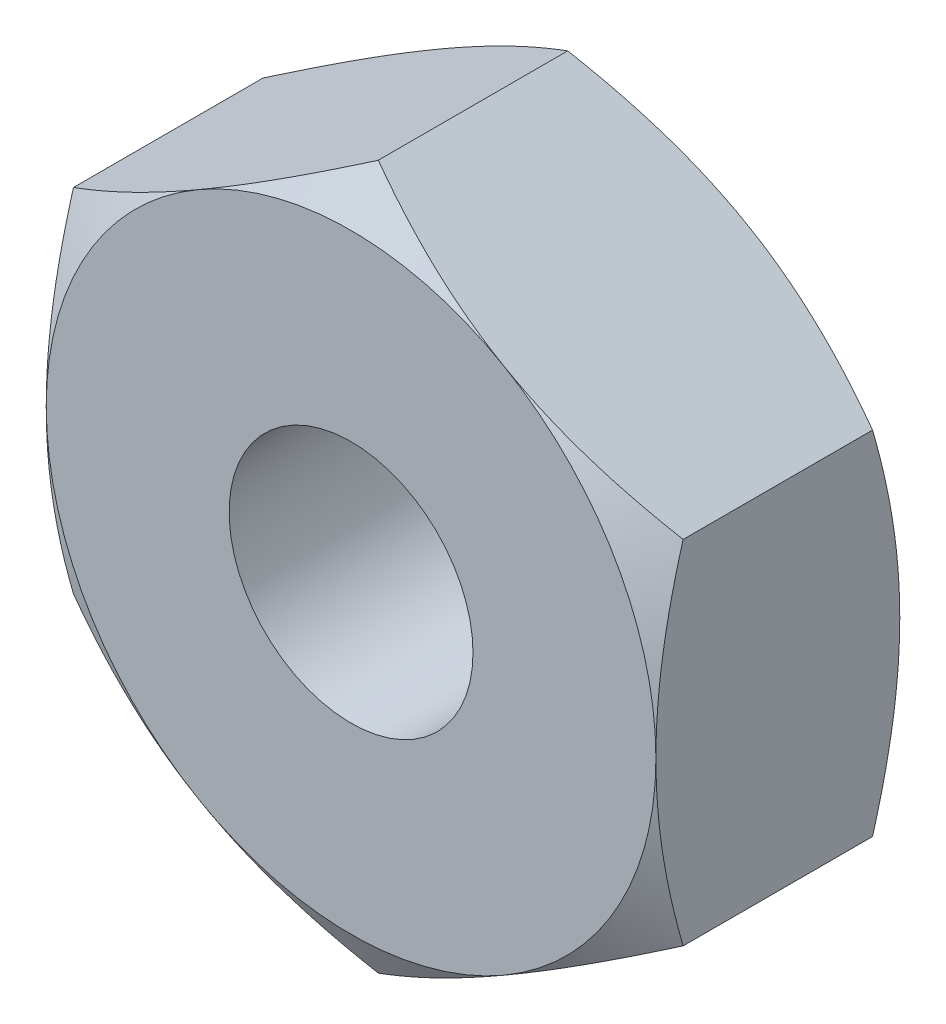
SolidWorks part; units mm, degrees
ref_plane "Front Plane" through (0, 0, 0) normal (0, 0, 1) x (1, 0, 0)
ref_plane "Top Plane" through (0, 0, 0) normal (0, 1, 0) x (1, 0, 0)
ref_plane "Right Plane" through (0, 0, 0) normal (1, 0, 0) x (0, 0, -1)
sketch "Sketch1" plane through (0, 0, 0) normal (0, 0, 1) x (1, 0, 0)
  line L1 (0, -2.8868) -> (2.5, -1.4434)
  line L2 (2.5, -1.4434) -> (2.5, 1.4434)
  line L3 (2.5, 1.4434) -> (0, 2.8868)
  line L4 (0, 2.8868) -> (-2.5, 1.4434)
  line L5 (-2.5, 1.4434) -> (-2.5, -1.4434)
  line L6 (-2.5, -1.4434) -> (0, -2.8868)
  circle A0 centre (0, 0) radius 1
  circle A1 centre (0, 0) radius 2.5 construction
  dimension "D1" = 5
  dimension "D2" = 2
extrude "Boss-Extrude1" add sketch "Sketch1" along normal blind 2
cosmetic thread "Cosmetic Thread1" parameters "D2"=4
sketch "Sketch2" plane through (0, 0, 2) normal (0, 0, 1) x (1, 0, 0)
  circle A0 centre (0, 0) radius 2.5 construction
  circle A1 centre (0, 0) radius 2.5
extrude "Cut-Extrude1" cut sketch "Sketch2" against normal blind 2 draft 60 flip side to cut
sketch "Sketch3" plane through (0, 0, 0) normal (0, 0, -1) x (-1, 0, 0)
  circle A0 centre (0, 0) radius 2.5 construction
  circle A1 centre (0, 0) radius 2.5
extrude "Cut-Extrude2" cut sketch "Sketch3" against normal blind 2 draft 60 flip side to cut
